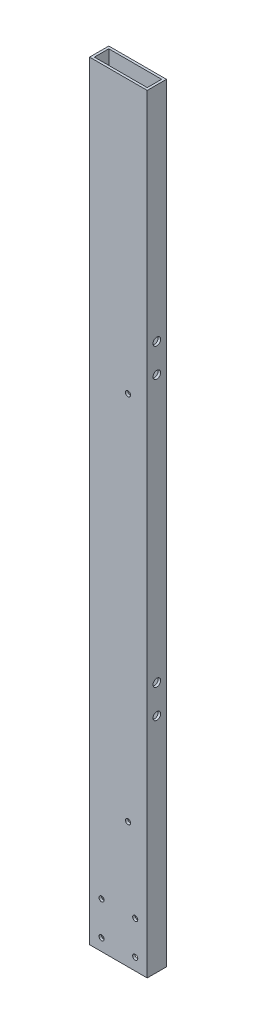
SolidWorks part; units mm, degrees
material "6061-T6 (SS)"
ref_plane "Front Plane" through (0, 0, 0) normal (0, 0, 1) x (1, 0, 0)
ref_plane "Top Plane" through (0, 0, 0) normal (0, 1, 0) x (1, 0, 0)
ref_plane "Right Plane" through (0, 0, 0) normal (1, 0, 0) x (0, 0, -1)
sketch "Sketch1" plane through (0, 0, 0) normal (0, 1, 0) x (1, 0, 0)
  line L0 (3.175, 3.175) -> (73.025, 3.175)
  line L1 (0, 0) -> (76.2, 0)
  line L2 (0, 0) -> (0, 25.4)
  line L3 (0, 25.4) -> (76.2, 25.4)
  line L4 (76.2, 0) -> (76.2, 25.4)
  line L5 (73.025, 3.175) -> (73.025, 22.225)
  line L6 (3.175, 22.225) -> (73.025, 22.225)
  line L7 (3.175, 3.175) -> (3.175, 22.225)
  dimension "D1" = 76.2
  dimension "D2" = 25.4
  dimension "D3" = 3.175
extrude "Boss-Extrude1" add sketch "Sketch1" along normal blind 1016
sketch "Sketch2" plane through (76.2, 0, 0) normal (1, 0, 0) x (0, 0, -1)
  line L0 (25.4, 1016) -> (25.4, 0) construction
  line L1 (115.6462, 350.8375) -> (-62.1538, 350.8375) construction
  circle A0 centre (12.7, 293.6875) radius 5.0419
  circle A1 centre (12.7, 331.7875) radius 5.0419
  dimension "D1" = 10.0838
  dimension "D2" = 10.0838
  dimension "D6" = 19.05
  dimension "D3" = 12.7
  dimension "D4" = 12.7
  dimension "D5" = 38.1
extrude "Cut-Extrude1" cut sketch "Sketch2" against normal through all
ref_plane "Plane1" through (0, 508, 0) normal (0, -1, 0) x (-1, 0, 0)
mirror "Mirror1" about plane through (0, 508, 0) normal (0, -1, 0) of "Cut-Extrude1"
sketch "Sketch3" plane through (0, 0, 0) normal (0, 0, 1) x (1, 0, 0)
  circle A0 centre (15.875, 15.875) radius 3.3782
  circle A1 centre (15.875, 60.325) radius 3.3782
  circle A2 centre (60.325, 15.875) radius 3.3782
  circle A3 centre (60.325, 60.325) radius 3.3782
  dimension "D1" = 6.7564
  dimension "D2" = 6.7564
  dimension "D3" = 6.7564
  dimension "D4" = 6.7564
extrude "Cut-Extrude2" cut sketch "Sketch3" against normal through all
sketch "Sketch4" plane through (0, 0, 0) normal (0, 0, 1) x (1, 0, 0)
  circle A0 centre (50.8, 166.2938) radius 3.3782
  circle A1 centre (50.8, 656.0312) radius 3.3782
  dimension "D1" = 6.7564
  dimension "D2" = 6.7564
extrude "Cut-Extrude3" cut sketch "Sketch4" against normal through all
